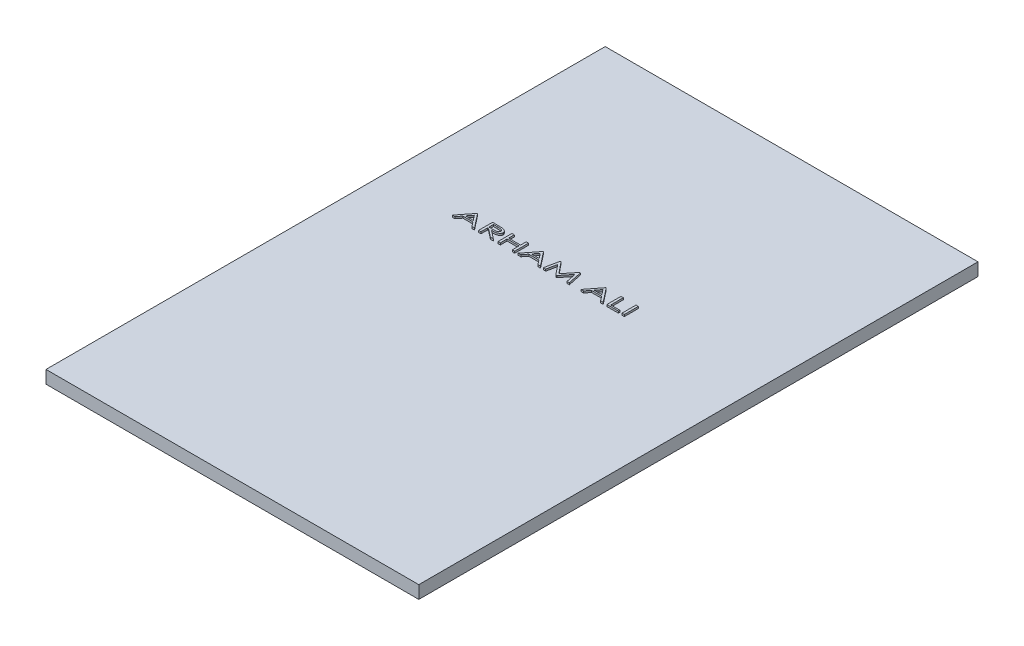
SolidWorks part; units mm, degrees
ref_plane "Front Plane" through (0, 0, 0) normal (0, 0, 1) x (1, 0, 0)
ref_plane "Top Plane" through (0, 0, 0) normal (0, 1, 0) x (1, 0, 0)
ref_plane "Right Plane" through (0, 0, 0) normal (1, 0, 0) x (0, 0, -1)
sketch "Sketch2" plane through (0, 0, 0) normal (0, 1, 0) x (1, 0, 0)
  line L1 (0, 0) -> (508, 0)
  line L2 (0, 0) -> (0, 762)
  line L3 (0, 762) -> (508, 762)
  line L4 (508, 0) -> (508, 762)
  dimension "D1" = 508
  dimension "D2" = 762
extrude "Boss-Extrude1" add sketch "Sketch2" along normal blind 20 contours L3 L4 L1 L2
sketch "Sketch6" plane through (0, 20, 0) normal (0, 1, 0) x (1, 0, 0)
  text T0 "ARHAM ALI" font "Century Gothic" height in points 72
extrude "Cut-Extrude3" cut sketch "Sketch6" against normal blind 2.54 flip side to cut
